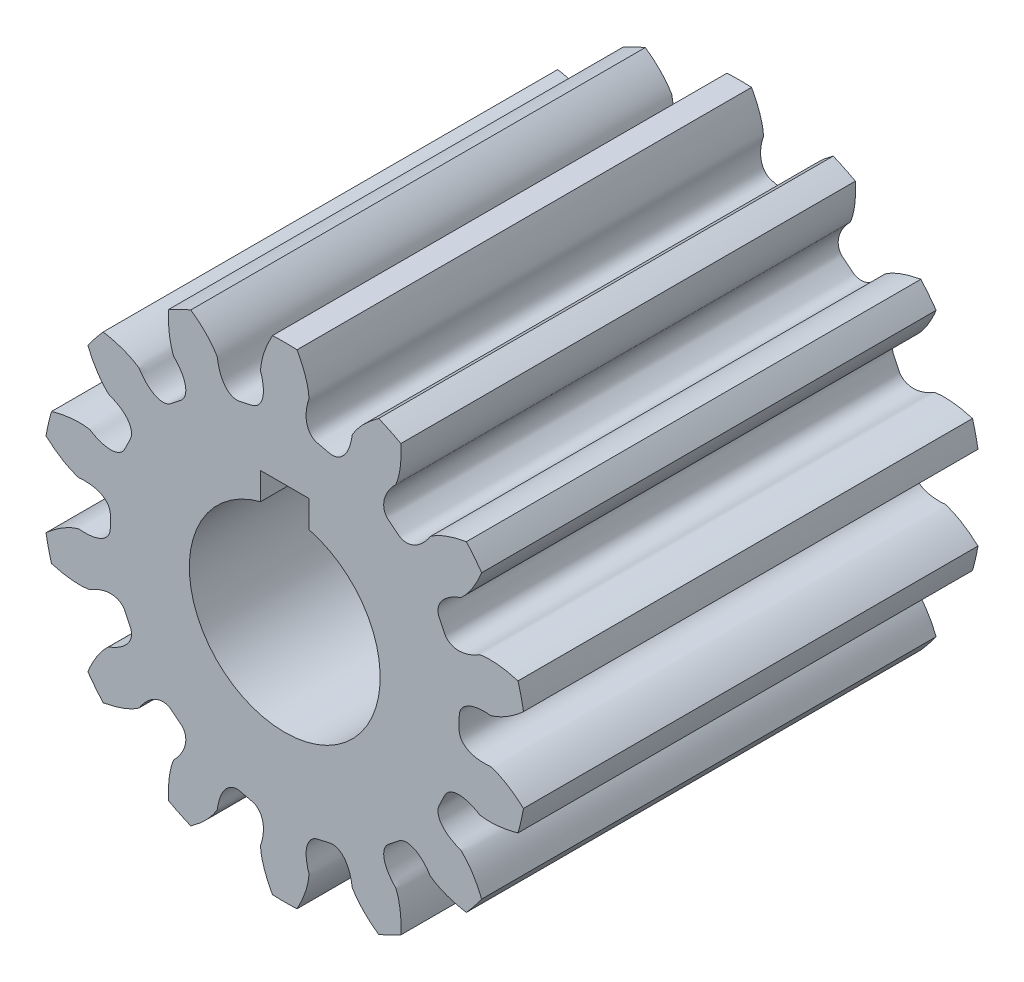
SolidWorks part; units mm, degrees
ref_plane "Front Plane" through (0, 0, 0) normal (0, 0, 1) x (1, 0, 0)
ref_plane "Top Plane" through (0, 0, 0) normal (0, 1, 0) x (1, 0, 0)
ref_plane "Right Plane" through (0, 0, 0) normal (1, 0, 0) x (0, 0, -1)
ref_plane "Plane1" through (0, 0, 9.525) normal (0, 0, 1) x (1, 0, 0)
sketch "Sketch1" plane through (0, 0, 9.525) normal (0, 0, 1) x (1, 0, 0)
  line L0 (1.01, 5) -> (1.01, 3.8704)
  line L1 (-1.01, 3.8704) -> (-1.01, 5)
  line L2 (-1.01, 5) -> (1.01, 5)
  arc A0 (1.01, 3.8704) -> (-1.01, 3.8704) centre (0, 0) cw
  arc A1 (8.2542, 5.9239) -> (7.6122, 6.7291) centre (0, 0) ccw
  arc A2 (4.8665, 8.9187) -> (3.9387, 9.3655) centre (0, 0) ccw
  arc A3 (0.5149, 10.1469) -> (-0.5149, 10.1469) centre (0, 0) ccw
  arc A4 (-3.9387, 9.3655) -> (-4.8665, 8.9187) centre (0, 0) ccw
  arc A5 (-7.6122, 6.7291) -> (-8.2542, 5.9239) centre (0, 0) ccw
  arc A6 (-9.778, 2.7599) -> (-10.0071, 1.7559) centre (0, 0) ccw
  arc A7 (-10.0071, -1.7559) -> (-9.778, -2.7599) centre (0, 0) ccw
  arc A8 (-8.2542, -5.9239) -> (-7.6122, -6.7291) centre (0, 0) ccw
  arc A9 (-4.8665, -8.9187) -> (-3.9387, -9.3655) centre (0, 0) ccw
  arc A10 (-0.5149, -10.1469) -> (0.5149, -10.1469) centre (0, 0) ccw
  arc A11 (3.9387, -9.3655) -> (4.8665, -8.9187) centre (0, 0) ccw
  arc A12 (7.6122, -6.7291) -> (8.2542, -5.9239) centre (0, 0) ccw
  arc A13 (9.778, -2.7599) -> (10.0071, -1.7559) centre (0, 0) ccw
  arc A14 (10.0071, 1.7559) -> (9.778, 2.7599) centre (0, 0) ccw
  spline S0 degree 3 poles (8.2542, 5.9239) (8.2213, 5.8435) (8.1658, 5.7165) (8.0838, 5.5483) (8.0156, 5.4193) (7.9477, 5.3002) (7.8807, 5.1908) (7.8151, 5.0911) (7.7514, 5.0008) (7.6901, 4.9196) (7.6319, 4.8472) (7.5771, 4.7835) (7.5263, 4.7282) (7.4801, 4.6804) (7.4277, 4.6319) (7.3617, 4.5626) (7.2605, 4.5412) (7.1763, 4.501) (7.1095, 4.4698) (7.046, 4.4368) (6.9852, 4.4028) (6.9274, 4.3677) (6.8725, 4.3315) (6.8204, 4.2943) (6.7711, 4.2559) (6.7247, 4.2165) (6.681, 4.1758) (6.64, 4.1337) (6.6019, 4.0902) (6.5666, 4.045) (6.5342, 3.9978) (6.5048, 3.9483) (6.4789, 3.8961) (6.4567, 3.8408) (6.4391, 3.782) (6.4268, 3.7194) (6.4213, 3.6531) (6.4238, 3.5836) (6.4357, 3.5122) (6.4562, 3.4476) (6.5069, 3.3338) (6.5953, 3.1761) (6.6635, 3.0087) (6.7208, 2.8982) (6.7585, 2.8418) (6.807, 2.788) (6.8597, 2.7427) (6.915, 2.7057) (6.9716, 2.6762) (7.0286, 2.6533) (7.0856, 2.6362) (7.1426, 2.6239) (7.1996, 2.616) (7.2567, 2.6119) (7.3141, 2.6114) (7.3719, 2.6141) (7.4303, 2.6199) (7.4893, 2.6286) (7.5492, 2.6404) (7.6099, 2.655) (7.6715, 2.6725) (7.734, 2.6929) (7.7975, 2.7162) (7.8619, 2.7424) (7.9273, 2.7715) (7.9934, 2.8043) (8.0773, 2.8451) (8.1571, 2.9109) (8.2524, 2.9193) (8.3231, 2.93) (8.3892, 2.9363) (8.4642, 2.9416) (8.5481, 2.9446) (8.641, 2.9451) (8.7427, 2.9423) (8.853, 2.9358) (8.9719, 2.9249) (9.0992, 2.9092) (9.2346, 2.888) (9.378, 2.8608) (9.5607, 2.8201) (9.6945, 2.7844) (9.778, 2.7599) knots 0.010403 0.010403 0.010403 0.010403 0.046486 0.067894 0.088079 0.107041 0.124779 0.141294 0.156585 0.170653 0.183498 0.19512 0.205518 0.214693 0.222644 0.235305 0.253444 0.263936 0.274129 0.28403 0.293651 0.303001 0.312093 0.320945 0.329573 0.337998 0.346246 0.354347 0.362336 0.370253 0.378149 0.386081 0.394114 0.402321 0.410779 0.419564 0.428738 0.438336 0.448346 0.458697 0.466397 0.5 0.533603 0.541303 0.551654 0.561664 0.571262 0.580436 0.589221 0.597679 0.605886 0.613919 0.621851 0.629747 0.637664 0.645653 0.653754 0.662002 0.670427 0.679055 0.687907 0.696999 0.706349 0.71597 0.725871 0.736064 0.746556 0.764695 0.777356 0.785307 0.794482 0.80488 0.816502 0.829347 0.843415 0.858706 0.875221 0.892959 0.911921 0.932106 0.953514 0.989597 0.989597 0.989597 0.989597
  spline S1 degree 3 poles (4.8665, 8.9187) (4.8718, 8.8319) (4.8769, 8.6934) (4.8759, 8.5062) (4.8705, 8.3604) (4.861, 8.2237) (4.848, 8.0961) (4.8322, 7.9778) (4.814, 7.8687) (4.7941, 7.769) (4.773, 7.6786) (4.7513, 7.5974) (4.7295, 7.5255) (4.7086, 7.4624) (4.6824, 7.3959) (4.653, 7.3049) (4.5711, 7.2417) (4.5127, 7.169) (4.466, 7.1119) (4.4231, 7.0545) (4.3832, 6.9976) (4.3463, 6.9409) (4.3125, 6.8844) (4.2818, 6.8283) (4.254, 6.7724) (4.2293, 6.7166) (4.2076, 6.661) (4.1889, 6.6054) (4.1734, 6.5496) (4.1612, 6.4936) (4.1525, 6.437) (4.1475, 6.3797) (4.1468, 6.3214) (4.1508, 6.2619) (4.1604, 6.2013) (4.1766, 6.1396) (4.2003, 6.0774) (4.2327, 6.0159) (4.2744, 5.9567) (4.321, 5.9074) (4.416, 5.8269) (4.5641, 5.7232) (4.6981, 5.6019) (4.7978, 5.5272) (4.8562, 5.4928) (4.9232, 5.4653) (4.9904, 5.4474) (5.0563, 5.4381) (5.12, 5.436) (5.1813, 5.4402) (5.2401, 5.4494) (5.2968, 5.4631) (5.3516, 5.4807) (5.4048, 5.5018) (5.4567, 5.5262) (5.5076, 5.5537) (5.5577, 5.5843) (5.6071, 5.6178) (5.656, 5.6543) (5.7043, 5.6938) (5.7522, 5.7363) (5.7997, 5.7818) (5.8468, 5.8304) (5.8934, 5.882) (5.9398, 5.9366) (5.985, 5.9948) (6.043, 6.0679) (6.0863, 6.1618) (6.1686, 6.2108) (6.2276, 6.2511) (6.2844, 6.2855) (6.3496, 6.3227) (6.424, 6.3619) (6.5074, 6.4026) (6.6002, 6.4442) (6.7025, 6.4862) (6.8143, 6.528) (6.9358, 6.5691) (7.067, 6.6087) (7.208, 6.6465) (7.3902, 6.6891) (7.5264, 6.7149) (7.6122, 6.7291) knots 0.010403 0.010403 0.010403 0.010403 0.046486 0.067894 0.088079 0.107041 0.124779 0.141294 0.156585 0.170653 0.183498 0.19512 0.205518 0.214693 0.222644 0.235305 0.253444 0.263936 0.274129 0.28403 0.293651 0.303001 0.312093 0.320945 0.329573 0.337998 0.346246 0.354347 0.362336 0.370253 0.378149 0.386081 0.394114 0.402321 0.410779 0.419564 0.428738 0.438336 0.448346 0.458697 0.466397 0.5 0.533603 0.541303 0.551654 0.561664 0.571262 0.580436 0.589221 0.597679 0.605886 0.613919 0.621851 0.629747 0.637664 0.645653 0.653754 0.662002 0.670427 0.679055 0.687907 0.696999 0.706349 0.71597 0.725871 0.736064 0.746556 0.764695 0.777356 0.785307 0.794482 0.80488 0.816502 0.829347 0.843415 0.858706 0.875221 0.892959 0.911921 0.932106 0.953514 0.989597 0.989597 0.989597 0.989597
  spline S2 degree 3 poles (0.5149, 10.1469) (0.5573, 10.071) (0.622, 9.9485) (0.7023, 9.7794) (0.7607, 9.6457) (0.8115, 9.5184) (0.8552, 9.3978) (0.8922, 9.2843) (0.9231, 9.1782) (0.9485, 9.0797) (0.9687, 8.9891) (0.9844, 8.9065) (0.9959, 8.8323) (1.0044, 8.7664) (1.0098, 8.6951) (1.0228, 8.6003) (0.9764, 8.5079) (0.9553, 8.417) (0.938, 8.3453) (0.9243, 8.275) (0.913, 8.2064) (0.9044, 8.1393) (0.8984, 8.0738) (0.8951, 8.0099) (0.8943, 7.9474) (0.8962, 7.8865) (0.9008, 7.8269) (0.9081, 7.7687) (0.9183, 7.7118) (0.9317, 7.656) (0.9483, 7.6012) (0.9688, 7.5474) (0.9934, 7.4946) (1.0228, 7.4428) (1.0578, 7.3923) (1.0991, 7.3437) (1.1475, 7.298) (1.2034, 7.2567) (1.2666, 7.2215) (1.33, 7.1972) (1.4505, 7.1659) (1.6289, 7.1367) (1.8023, 7.0856) (1.9245, 7.0615) (1.9921, 7.0559) (2.0644, 7.0602) (2.1327, 7.0732) (2.1961, 7.0934) (2.2544, 7.1192) (2.3078, 7.1495) (2.3568, 7.1834) (2.4019, 7.2203) (2.4436, 7.2599) (2.4824, 7.302) (2.5186, 7.3465) (2.5526, 7.3934) (2.5844, 7.4427) (2.6144, 7.4943) (2.6425, 7.5484) (2.6689, 7.605) (2.6937, 7.6641) (2.7167, 7.7257) (2.7381, 7.7898) (2.7577, 7.8566) (2.7758, 7.9259) (2.7913, 7.998) (2.8117, 8.089) (2.8101, 8.1924) (2.8629, 8.2722) (2.8986, 8.3341) (2.9349, 8.3897) (2.9775, 8.4516) (3.0275, 8.5192) (3.085, 8.592) (3.1505, 8.6698) (3.2245, 8.752) (3.3071, 8.8382) (3.3987, 8.9279) (3.4997, 9.0205) (3.6104, 9.1157) (3.7561, 9.2331) (3.8675, 9.3155) (3.9387, 9.3655) knots 0.010403 0.010403 0.010403 0.010403 0.046486 0.067894 0.088079 0.107041 0.124779 0.141294 0.156585 0.170653 0.183498 0.19512 0.205518 0.214693 0.222644 0.235305 0.253444 0.263936 0.274129 0.28403 0.293651 0.303001 0.312093 0.320945 0.329573 0.337998 0.346246 0.354347 0.362336 0.370253 0.378149 0.386081 0.394114 0.402321 0.410779 0.419564 0.428738 0.438336 0.448346 0.458697 0.466397 0.5 0.533603 0.541303 0.551654 0.561664 0.571262 0.580436 0.589221 0.597679 0.605886 0.613919 0.621851 0.629747 0.637664 0.645653 0.653754 0.662002 0.670427 0.679055 0.687907 0.696999 0.706349 0.71597 0.725871 0.736064 0.746556 0.764695 0.777356 0.785307 0.794482 0.80488 0.816502 0.829347 0.843415 0.858706 0.875221 0.892959 0.911921 0.932106 0.953514 0.989597 0.989597 0.989597 0.989597
  spline S3 degree 3 poles (-3.9387, 9.3655) (-3.8675, 9.3155) (-3.7561, 9.2331) (-3.6104, 9.1157) (-3.4997, 9.0205) (-3.3987, 8.9279) (-3.3071, 8.8382) (-3.2245, 8.752) (-3.1505, 8.6698) (-3.085, 8.592) (-3.0275, 8.5192) (-2.9775, 8.4516) (-2.9349, 8.3897) (-2.8986, 8.3341) (-2.8629, 8.2722) (-2.8101, 8.1924) (-2.8117, 8.089) (-2.7913, 7.998) (-2.7758, 7.9259) (-2.7577, 7.8566) (-2.7381, 7.7898) (-2.7167, 7.7257) (-2.6937, 7.6641) (-2.6689, 7.605) (-2.6425, 7.5484) (-2.6144, 7.4943) (-2.5844, 7.4427) (-2.5526, 7.3934) (-2.5186, 7.3465) (-2.4824, 7.302) (-2.4436, 7.2599) (-2.4019, 7.2203) (-2.3568, 7.1834) (-2.3078, 7.1495) (-2.2544, 7.1192) (-2.1961, 7.0934) (-2.1327, 7.0732) (-2.0644, 7.0602) (-1.9921, 7.0559) (-1.9245, 7.0615) (-1.8023, 7.0856) (-1.6289, 7.1367) (-1.4505, 7.1659) (-1.33, 7.1972) (-1.2666, 7.2215) (-1.2034, 7.2567) (-1.1475, 7.298) (-1.0991, 7.3437) (-1.0578, 7.3923) (-1.0228, 7.4428) (-0.9934, 7.4946) (-0.9688, 7.5474) (-0.9483, 7.6012) (-0.9317, 7.656) (-0.9183, 7.7118) (-0.9081, 7.7687) (-0.9008, 7.8269) (-0.8962, 7.8865) (-0.8943, 7.9474) (-0.8951, 8.0099) (-0.8984, 8.0738) (-0.9044, 8.1393) (-0.913, 8.2064) (-0.9243, 8.275) (-0.938, 8.3453) (-0.9553, 8.417) (-0.9764, 8.5079) (-1.0228, 8.6003) (-1.0098, 8.6951) (-1.0044, 8.7664) (-0.9959, 8.8323) (-0.9844, 8.9065) (-0.9687, 8.9891) (-0.9485, 9.0797) (-0.9231, 9.1782) (-0.8922, 9.2843) (-0.8552, 9.3978) (-0.8115, 9.5184) (-0.7607, 9.6457) (-0.7023, 9.7794) (-0.622, 9.9485) (-0.5573, 10.071) (-0.5149, 10.1469) knots 0.010403 0.010403 0.010403 0.010403 0.046486 0.067894 0.088079 0.107041 0.124779 0.141294 0.156585 0.170653 0.183498 0.19512 0.205518 0.214693 0.222644 0.235305 0.253444 0.263936 0.274129 0.28403 0.293651 0.303001 0.312093 0.320945 0.329573 0.337998 0.346246 0.354347 0.362336 0.370253 0.378149 0.386081 0.394114 0.402321 0.410779 0.419564 0.428738 0.438336 0.448346 0.458697 0.466397 0.5 0.533603 0.541303 0.551654 0.561664 0.571262 0.580436 0.589221 0.597679 0.605886 0.613919 0.621851 0.629747 0.637664 0.645653 0.653754 0.662002 0.670427 0.679055 0.687907 0.696999 0.706349 0.71597 0.725871 0.736064 0.746556 0.764695 0.777356 0.785307 0.794482 0.80488 0.816502 0.829347 0.843415 0.858706 0.875221 0.892959 0.911921 0.932106 0.953514 0.989597 0.989597 0.989597 0.989597
  spline S4 degree 3 poles (-7.6122, 6.7291) (-7.5264, 6.7149) (-7.3902, 6.6891) (-7.208, 6.6465) (-7.067, 6.6087) (-6.9358, 6.5691) (-6.8143, 6.528) (-6.7025, 6.4862) (-6.6002, 6.4442) (-6.5074, 6.4026) (-6.424, 6.3619) (-6.3496, 6.3227) (-6.2844, 6.2855) (-6.2276, 6.2511) (-6.1686, 6.2108) (-6.0863, 6.1618) (-6.043, 6.0679) (-5.985, 5.9948) (-5.9398, 5.9366) (-5.8934, 5.882) (-5.8468, 5.8304) (-5.7997, 5.7818) (-5.7522, 5.7363) (-5.7043, 5.6938) (-5.656, 5.6543) (-5.6071, 5.6178) (-5.5577, 5.5843) (-5.5076, 5.5537) (-5.4567, 5.5262) (-5.4048, 5.5018) (-5.3516, 5.4807) (-5.2968, 5.4631) (-5.2401, 5.4494) (-5.1813, 5.4402) (-5.12, 5.436) (-5.0563, 5.4381) (-4.9904, 5.4474) (-4.9232, 5.4653) (-4.8562, 5.4928) (-4.7978, 5.5272) (-4.6981, 5.6019) (-4.5641, 5.7232) (-4.416, 5.8269) (-4.321, 5.9074) (-4.2744, 5.9567) (-4.2327, 6.0159) (-4.2003, 6.0774) (-4.1766, 6.1396) (-4.1604, 6.2013) (-4.1508, 6.2619) (-4.1468, 6.3214) (-4.1475, 6.3797) (-4.1525, 6.437) (-4.1612, 6.4936) (-4.1734, 6.5496) (-4.1889, 6.6054) (-4.2076, 6.661) (-4.2293, 6.7166) (-4.254, 6.7724) (-4.2818, 6.8283) (-4.3125, 6.8844) (-4.3463, 6.9409) (-4.3832, 6.9976) (-4.4231, 7.0545) (-4.466, 7.1119) (-4.5127, 7.169) (-4.5711, 7.2417) (-4.653, 7.3049) (-4.6824, 7.3959) (-4.7086, 7.4624) (-4.7295, 7.5255) (-4.7513, 7.5974) (-4.773, 7.6786) (-4.7941, 7.769) (-4.814, 7.8687) (-4.8322, 7.9778) (-4.848, 8.0961) (-4.861, 8.2237) (-4.8705, 8.3604) (-4.8759, 8.5062) (-4.8769, 8.6934) (-4.8718, 8.8319) (-4.8665, 8.9187) knots 0.010403 0.010403 0.010403 0.010403 0.046486 0.067894 0.088079 0.107041 0.124779 0.141294 0.156585 0.170653 0.183498 0.19512 0.205518 0.214693 0.222644 0.235305 0.253444 0.263936 0.274129 0.28403 0.293651 0.303001 0.312093 0.320945 0.329573 0.337998 0.346246 0.354347 0.362336 0.370253 0.378149 0.386081 0.394114 0.402321 0.410779 0.419564 0.428738 0.438336 0.448346 0.458697 0.466397 0.5 0.533603 0.541303 0.551654 0.561664 0.571262 0.580436 0.589221 0.597679 0.605886 0.613919 0.621851 0.629747 0.637664 0.645653 0.653754 0.662002 0.670427 0.679055 0.687907 0.696999 0.706349 0.71597 0.725871 0.736064 0.746556 0.764695 0.777356 0.785307 0.794482 0.80488 0.816502 0.829347 0.843415 0.858706 0.875221 0.892959 0.911921 0.932106 0.953514 0.989597 0.989597 0.989597 0.989597
  spline S5 degree 3 poles (-9.778, 2.7599) (-9.6945, 2.7844) (-9.5607, 2.8201) (-9.378, 2.8608) (-9.2346, 2.888) (-9.0992, 2.9092) (-8.9719, 2.9249) (-8.853, 2.9358) (-8.7427, 2.9423) (-8.641, 2.9451) (-8.5481, 2.9446) (-8.4642, 2.9416) (-8.3892, 2.9363) (-8.3231, 2.93) (-8.2524, 2.9193) (-8.1571, 2.9109) (-8.0773, 2.8451) (-7.9934, 2.8043) (-7.9273, 2.7715) (-7.8619, 2.7424) (-7.7975, 2.7162) (-7.734, 2.6929) (-7.6715, 2.6725) (-7.6099, 2.655) (-7.5492, 2.6404) (-7.4893, 2.6286) (-7.4303, 2.6199) (-7.3719, 2.6141) (-7.3141, 2.6114) (-7.2567, 2.6119) (-7.1996, 2.616) (-7.1426, 2.6239) (-7.0856, 2.6362) (-7.0286, 2.6533) (-6.9716, 2.6762) (-6.915, 2.7057) (-6.8597, 2.7427) (-6.807, 2.788) (-6.7585, 2.8418) (-6.7208, 2.8982) (-6.6635, 3.0087) (-6.5953, 3.1761) (-6.5069, 3.3338) (-6.4562, 3.4476) (-6.4357, 3.5122) (-6.4238, 3.5836) (-6.4213, 3.6531) (-6.4268, 3.7194) (-6.4391, 3.782) (-6.4567, 3.8408) (-6.4789, 3.8961) (-6.5048, 3.9483) (-6.5342, 3.9978) (-6.5666, 4.045) (-6.6019, 4.0902) (-6.64, 4.1337) (-6.681, 4.1758) (-6.7247, 4.2165) (-6.7711, 4.2559) (-6.8204, 4.2943) (-6.8725, 4.3315) (-6.9274, 4.3677) (-6.9852, 4.4028) (-7.046, 4.4368) (-7.1095, 4.4698) (-7.1763, 4.501) (-7.2605, 4.5412) (-7.3617, 4.5626) (-7.4277, 4.6319) (-7.4801, 4.6804) (-7.5263, 4.7282) (-7.5771, 4.7835) (-7.6319, 4.8472) (-7.6901, 4.9196) (-7.7514, 5.0008) (-7.8151, 5.0911) (-7.8807, 5.1908) (-7.9477, 5.3002) (-8.0156, 5.4193) (-8.0838, 5.5483) (-8.1658, 5.7165) (-8.2213, 5.8435) (-8.2542, 5.9239) knots 0.010403 0.010403 0.010403 0.010403 0.046486 0.067894 0.088079 0.107041 0.124779 0.141294 0.156585 0.170653 0.183498 0.19512 0.205518 0.214693 0.222644 0.235305 0.253444 0.263936 0.274129 0.28403 0.293651 0.303001 0.312093 0.320945 0.329573 0.337998 0.346246 0.354347 0.362336 0.370253 0.378149 0.386081 0.394114 0.402321 0.410779 0.419564 0.428738 0.438336 0.448346 0.458697 0.466397 0.5 0.533603 0.541303 0.551654 0.561664 0.571262 0.580436 0.589221 0.597679 0.605886 0.613919 0.621851 0.629747 0.637664 0.645653 0.653754 0.662002 0.670427 0.679055 0.687907 0.696999 0.706349 0.71597 0.725871 0.736064 0.746556 0.764695 0.777356 0.785307 0.794482 0.80488 0.816502 0.829347 0.843415 0.858706 0.875221 0.892959 0.911921 0.932106 0.953514 0.989597 0.989597 0.989597 0.989597
  spline S6 degree 3 poles (-10.0071, -1.7559) (-9.9426, -1.6977) (-9.8375, -1.6074) (-9.6905, -1.4914) (-9.5731, -1.4047) (-9.4603, -1.3269) (-9.3525, -1.2575) (-9.2501, -1.1961) (-9.1535, -1.1423) (-9.0631, -1.0957) (-8.9792, -1.0559) (-8.9023, -1.0222) (-8.8324, -0.9944) (-8.7701, -0.9714) (-8.7018, -0.9504) (-8.6123, -0.9166) (-8.5118, -0.9413) (-8.4186, -0.9416) (-8.3448, -0.9425) (-8.2732, -0.9403) (-8.2038, -0.936) (-8.1365, -0.9295) (-8.0713, -0.9207) (-8.0082, -0.9097) (-7.9472, -0.8966) (-7.8882, -0.8812) (-7.8311, -0.8635) (-7.776, -0.8434) (-7.7228, -0.8207) (-7.6713, -0.7953) (-7.6217, -0.7669) (-7.5738, -0.735) (-7.5277, -0.6992) (-7.4838, -0.659) (-7.4423, -0.6137) (-7.4042, -0.5626) (-7.3704, -0.5053) (-7.3425, -0.4416) (-7.3222, -0.3721) (-7.3127, -0.3049) (-7.309, -0.1804) (-7.3203, 0) (-7.309, 0.1804) (-7.3127, 0.3049) (-7.3222, 0.3721) (-7.3425, 0.4416) (-7.3704, 0.5053) (-7.4042, 0.5626) (-7.4423, 0.6137) (-7.4838, 0.659) (-7.5277, 0.6992) (-7.5738, 0.735) (-7.6217, 0.7669) (-7.6713, 0.7953) (-7.7228, 0.8207) (-7.776, 0.8434) (-7.8311, 0.8635) (-7.8882, 0.8812) (-7.9472, 0.8966) (-8.0082, 0.9097) (-8.0713, 0.9207) (-8.1365, 0.9295) (-8.2038, 0.936) (-8.2732, 0.9403) (-8.3448, 0.9425) (-8.4186, 0.9416) (-8.5118, 0.9413) (-8.6123, 0.9166) (-8.7018, 0.9504) (-8.7701, 0.9714) (-8.8324, 0.9944) (-8.9023, 1.0222) (-8.9792, 1.0559) (-9.0631, 1.0957) (-9.1535, 1.1423) (-9.2501, 1.1961) (-9.3525, 1.2575) (-9.4603, 1.3269) (-9.5731, 1.4047) (-9.6905, 1.4914) (-9.8375, 1.6074) (-9.9426, 1.6977) (-10.0071, 1.7559) knots 0.010403 0.010403 0.010403 0.010403 0.046486 0.067894 0.088079 0.107041 0.124779 0.141294 0.156585 0.170653 0.183498 0.19512 0.205518 0.214693 0.222644 0.235305 0.253444 0.263936 0.274129 0.28403 0.293651 0.303001 0.312093 0.320945 0.329573 0.337998 0.346246 0.354347 0.362336 0.370253 0.378149 0.386081 0.394114 0.402321 0.410779 0.419564 0.428738 0.438336 0.448346 0.458697 0.466397 0.5 0.533603 0.541303 0.551654 0.561664 0.571262 0.580436 0.589221 0.597679 0.605886 0.613919 0.621851 0.629747 0.637664 0.645653 0.653754 0.662002 0.670427 0.679055 0.687907 0.696999 0.706349 0.71597 0.725871 0.736064 0.746556 0.764695 0.777356 0.785307 0.794482 0.80488 0.816502 0.829347 0.843415 0.858706 0.875221 0.892959 0.911921 0.932106 0.953514 0.989597 0.989597 0.989597 0.989597
  spline S7 degree 3 poles (-8.2542, -5.9239) (-8.2213, -5.8435) (-8.1658, -5.7165) (-8.0838, -5.5483) (-8.0156, -5.4193) (-7.9477, -5.3002) (-7.8807, -5.1908) (-7.8151, -5.0911) (-7.7514, -5.0008) (-7.6901, -4.9196) (-7.6319, -4.8472) (-7.5771, -4.7835) (-7.5263, -4.7282) (-7.4801, -4.6804) (-7.4277, -4.6319) (-7.3617, -4.5626) (-7.2605, -4.5412) (-7.1763, -4.501) (-7.1095, -4.4698) (-7.046, -4.4368) (-6.9852, -4.4028) (-6.9274, -4.3677) (-6.8725, -4.3315) (-6.8204, -4.2943) (-6.7711, -4.2559) (-6.7247, -4.2165) (-6.681, -4.1758) (-6.64, -4.1337) (-6.6019, -4.0902) (-6.5666, -4.045) (-6.5342, -3.9978) (-6.5048, -3.9483) (-6.4789, -3.8961) (-6.4567, -3.8408) (-6.4391, -3.782) (-6.4268, -3.7194) (-6.4213, -3.6531) (-6.4238, -3.5836) (-6.4357, -3.5122) (-6.4562, -3.4476) (-6.5069, -3.3338) (-6.5953, -3.1761) (-6.6635, -3.0087) (-6.7208, -2.8982) (-6.7585, -2.8418) (-6.807, -2.788) (-6.8597, -2.7427) (-6.915, -2.7057) (-6.9716, -2.6762) (-7.0286, -2.6533) (-7.0856, -2.6362) (-7.1426, -2.6239) (-7.1996, -2.616) (-7.2567, -2.6119) (-7.3141, -2.6114) (-7.3719, -2.6141) (-7.4303, -2.6199) (-7.4893, -2.6286) (-7.5492, -2.6404) (-7.6099, -2.655) (-7.6715, -2.6725) (-7.734, -2.6929) (-7.7975, -2.7162) (-7.8619, -2.7424) (-7.9273, -2.7715) (-7.9934, -2.8043) (-8.0773, -2.8451) (-8.1571, -2.9109) (-8.2524, -2.9193) (-8.3231, -2.93) (-8.3892, -2.9363) (-8.4642, -2.9416) (-8.5481, -2.9446) (-8.641, -2.9451) (-8.7427, -2.9423) (-8.853, -2.9358) (-8.9719, -2.9249) (-9.0992, -2.9092) (-9.2346, -2.888) (-9.378, -2.8608) (-9.5607, -2.8201) (-9.6945, -2.7844) (-9.778, -2.7599) knots 0.010403 0.010403 0.010403 0.010403 0.046486 0.067894 0.088079 0.107041 0.124779 0.141294 0.156585 0.170653 0.183498 0.19512 0.205518 0.214693 0.222644 0.235305 0.253444 0.263936 0.274129 0.28403 0.293651 0.303001 0.312093 0.320945 0.329573 0.337998 0.346246 0.354347 0.362336 0.370253 0.378149 0.386081 0.394114 0.402321 0.410779 0.419564 0.428738 0.438336 0.448346 0.458697 0.466397 0.5 0.533603 0.541303 0.551654 0.561664 0.571262 0.580436 0.589221 0.597679 0.605886 0.613919 0.621851 0.629747 0.637664 0.645653 0.653754 0.662002 0.670427 0.679055 0.687907 0.696999 0.706349 0.71597 0.725871 0.736064 0.746556 0.764695 0.777356 0.785307 0.794482 0.80488 0.816502 0.829347 0.843415 0.858706 0.875221 0.892959 0.911921 0.932106 0.953514 0.989597 0.989597 0.989597 0.989597
  spline S8 degree 3 poles (-4.8665, -8.9187) (-4.8718, -8.8319) (-4.8769, -8.6934) (-4.8759, -8.5062) (-4.8705, -8.3604) (-4.861, -8.2237) (-4.848, -8.0961) (-4.8322, -7.9778) (-4.814, -7.8687) (-4.7941, -7.769) (-4.773, -7.6786) (-4.7513, -7.5974) (-4.7295, -7.5255) (-4.7086, -7.4624) (-4.6824, -7.3959) (-4.653, -7.3049) (-4.5711, -7.2417) (-4.5127, -7.169) (-4.466, -7.1119) (-4.4231, -7.0545) (-4.3832, -6.9976) (-4.3463, -6.9409) (-4.3125, -6.8844) (-4.2818, -6.8283) (-4.254, -6.7724) (-4.2293, -6.7166) (-4.2076, -6.661) (-4.1889, -6.6054) (-4.1734, -6.5496) (-4.1612, -6.4936) (-4.1525, -6.437) (-4.1475, -6.3797) (-4.1468, -6.3214) (-4.1508, -6.2619) (-4.1604, -6.2013) (-4.1766, -6.1396) (-4.2003, -6.0774) (-4.2327, -6.0159) (-4.2744, -5.9567) (-4.321, -5.9074) (-4.416, -5.8269) (-4.5641, -5.7232) (-4.6981, -5.6019) (-4.7978, -5.5272) (-4.8562, -5.4928) (-4.9232, -5.4653) (-4.9904, -5.4474) (-5.0563, -5.4381) (-5.12, -5.436) (-5.1813, -5.4402) (-5.2401, -5.4494) (-5.2968, -5.4631) (-5.3516, -5.4807) (-5.4048, -5.5018) (-5.4567, -5.5262) (-5.5076, -5.5537) (-5.5577, -5.5843) (-5.6071, -5.6178) (-5.656, -5.6543) (-5.7043, -5.6938) (-5.7522, -5.7363) (-5.7997, -5.7818) (-5.8468, -5.8304) (-5.8934, -5.882) (-5.9398, -5.9366) (-5.985, -5.9948) (-6.043, -6.0679) (-6.0863, -6.1618) (-6.1686, -6.2108) (-6.2276, -6.2511) (-6.2844, -6.2855) (-6.3496, -6.3227) (-6.424, -6.3619) (-6.5074, -6.4026) (-6.6002, -6.4442) (-6.7025, -6.4862) (-6.8143, -6.528) (-6.9358, -6.5691) (-7.067, -6.6087) (-7.208, -6.6465) (-7.3902, -6.6891) (-7.5264, -6.7149) (-7.6122, -6.7291) knots 0.010403 0.010403 0.010403 0.010403 0.046486 0.067894 0.088079 0.107041 0.124779 0.141294 0.156585 0.170653 0.183498 0.19512 0.205518 0.214693 0.222644 0.235305 0.253444 0.263936 0.274129 0.28403 0.293651 0.303001 0.312093 0.320945 0.329573 0.337998 0.346246 0.354347 0.362336 0.370253 0.378149 0.386081 0.394114 0.402321 0.410779 0.419564 0.428738 0.438336 0.448346 0.458697 0.466397 0.5 0.533603 0.541303 0.551654 0.561664 0.571262 0.580436 0.589221 0.597679 0.605886 0.613919 0.621851 0.629747 0.637664 0.645653 0.653754 0.662002 0.670427 0.679055 0.687907 0.696999 0.706349 0.71597 0.725871 0.736064 0.746556 0.764695 0.777356 0.785307 0.794482 0.80488 0.816502 0.829347 0.843415 0.858706 0.875221 0.892959 0.911921 0.932106 0.953514 0.989597 0.989597 0.989597 0.989597
  spline S9 degree 3 poles (-0.5149, -10.1469) (-0.5573, -10.071) (-0.622, -9.9485) (-0.7023, -9.7794) (-0.7607, -9.6457) (-0.8115, -9.5184) (-0.8552, -9.3978) (-0.8922, -9.2843) (-0.9231, -9.1782) (-0.9485, -9.0797) (-0.9687, -8.9891) (-0.9844, -8.9065) (-0.9959, -8.8323) (-1.0044, -8.7664) (-1.0098, -8.6951) (-1.0228, -8.6003) (-0.9764, -8.5079) (-0.9553, -8.417) (-0.938, -8.3453) (-0.9243, -8.275) (-0.913, -8.2064) (-0.9044, -8.1393) (-0.8984, -8.0738) (-0.8951, -8.0099) (-0.8943, -7.9474) (-0.8962, -7.8865) (-0.9008, -7.8269) (-0.9081, -7.7687) (-0.9183, -7.7118) (-0.9317, -7.656) (-0.9483, -7.6012) (-0.9688, -7.5474) (-0.9934, -7.4946) (-1.0228, -7.4428) (-1.0578, -7.3923) (-1.0991, -7.3437) (-1.1475, -7.298) (-1.2034, -7.2567) (-1.2666, -7.2215) (-1.33, -7.1972) (-1.4505, -7.1659) (-1.6289, -7.1367) (-1.8023, -7.0856) (-1.9245, -7.0615) (-1.9921, -7.0559) (-2.0644, -7.0602) (-2.1327, -7.0732) (-2.1961, -7.0934) (-2.2544, -7.1192) (-2.3078, -7.1495) (-2.3568, -7.1834) (-2.4019, -7.2203) (-2.4436, -7.2599) (-2.4824, -7.302) (-2.5186, -7.3465) (-2.5526, -7.3934) (-2.5844, -7.4427) (-2.6144, -7.4943) (-2.6425, -7.5484) (-2.6689, -7.605) (-2.6937, -7.6641) (-2.7167, -7.7257) (-2.7381, -7.7898) (-2.7577, -7.8566) (-2.7758, -7.9259) (-2.7913, -7.998) (-2.8117, -8.089) (-2.8101, -8.1924) (-2.8629, -8.2722) (-2.8986, -8.3341) (-2.9349, -8.3897) (-2.9775, -8.4516) (-3.0275, -8.5192) (-3.085, -8.592) (-3.1505, -8.6698) (-3.2245, -8.752) (-3.3071, -8.8382) (-3.3987, -8.9279) (-3.4997, -9.0205) (-3.6104, -9.1157) (-3.7561, -9.2331) (-3.8675, -9.3155) (-3.9387, -9.3655) knots 0.010403 0.010403 0.010403 0.010403 0.046486 0.067894 0.088079 0.107041 0.124779 0.141294 0.156585 0.170653 0.183498 0.19512 0.205518 0.214693 0.222644 0.235305 0.253444 0.263936 0.274129 0.28403 0.293651 0.303001 0.312093 0.320945 0.329573 0.337998 0.346246 0.354347 0.362336 0.370253 0.378149 0.386081 0.394114 0.402321 0.410779 0.419564 0.428738 0.438336 0.448346 0.458697 0.466397 0.5 0.533603 0.541303 0.551654 0.561664 0.571262 0.580436 0.589221 0.597679 0.605886 0.613919 0.621851 0.629747 0.637664 0.645653 0.653754 0.662002 0.670427 0.679055 0.687907 0.696999 0.706349 0.71597 0.725871 0.736064 0.746556 0.764695 0.777356 0.785307 0.794482 0.80488 0.816502 0.829347 0.843415 0.858706 0.875221 0.892959 0.911921 0.932106 0.953514 0.989597 0.989597 0.989597 0.989597
  spline S10 degree 3 poles (3.9387, -9.3655) (3.8675, -9.3155) (3.7561, -9.2331) (3.6104, -9.1157) (3.4997, -9.0205) (3.3987, -8.9279) (3.3071, -8.8382) (3.2245, -8.752) (3.1505, -8.6698) (3.085, -8.592) (3.0275, -8.5192) (2.9775, -8.4516) (2.9349, -8.3897) (2.8986, -8.3341) (2.8629, -8.2722) (2.8101, -8.1924) (2.8117, -8.089) (2.7913, -7.998) (2.7758, -7.9259) (2.7577, -7.8566) (2.7381, -7.7898) (2.7167, -7.7257) (2.6937, -7.6641) (2.6689, -7.605) (2.6425, -7.5484) (2.6144, -7.4943) (2.5844, -7.4427) (2.5526, -7.3934) (2.5186, -7.3465) (2.4824, -7.302) (2.4436, -7.2599) (2.4019, -7.2203) (2.3568, -7.1834) (2.3078, -7.1495) (2.2544, -7.1192) (2.1961, -7.0934) (2.1327, -7.0732) (2.0644, -7.0602) (1.9921, -7.0559) (1.9245, -7.0615) (1.8023, -7.0856) (1.6289, -7.1367) (1.4505, -7.1659) (1.33, -7.1972) (1.2666, -7.2215) (1.2034, -7.2567) (1.1475, -7.298) (1.0991, -7.3437) (1.0578, -7.3923) (1.0228, -7.4428) (0.9934, -7.4946) (0.9688, -7.5474) (0.9483, -7.6012) (0.9317, -7.656) (0.9183, -7.7118) (0.9081, -7.7687) (0.9008, -7.8269) (0.8962, -7.8865) (0.8943, -7.9474) (0.8951, -8.0099) (0.8984, -8.0738) (0.9044, -8.1393) (0.913, -8.2064) (0.9243, -8.275) (0.938, -8.3453) (0.9553, -8.417) (0.9764, -8.5079) (1.0228, -8.6003) (1.0098, -8.6951) (1.0044, -8.7664) (0.9959, -8.8323) (0.9844, -8.9065) (0.9687, -8.9891) (0.9485, -9.0797) (0.9231, -9.1782) (0.8922, -9.2843) (0.8552, -9.3978) (0.8115, -9.5184) (0.7607, -9.6457) (0.7023, -9.7794) (0.622, -9.9485) (0.5573, -10.071) (0.5149, -10.1469) knots 0.010403 0.010403 0.010403 0.010403 0.046486 0.067894 0.088079 0.107041 0.124779 0.141294 0.156585 0.170653 0.183498 0.19512 0.205518 0.214693 0.222644 0.235305 0.253444 0.263936 0.274129 0.28403 0.293651 0.303001 0.312093 0.320945 0.329573 0.337998 0.346246 0.354347 0.362336 0.370253 0.378149 0.386081 0.394114 0.402321 0.410779 0.419564 0.428738 0.438336 0.448346 0.458697 0.466397 0.5 0.533603 0.541303 0.551654 0.561664 0.571262 0.580436 0.589221 0.597679 0.605886 0.613919 0.621851 0.629747 0.637664 0.645653 0.653754 0.662002 0.670427 0.679055 0.687907 0.696999 0.706349 0.71597 0.725871 0.736064 0.746556 0.764695 0.777356 0.785307 0.794482 0.80488 0.816502 0.829347 0.843415 0.858706 0.875221 0.892959 0.911921 0.932106 0.953514 0.989597 0.989597 0.989597 0.989597
  spline S11 degree 3 poles (7.6122, -6.7291) (7.5264, -6.7149) (7.3902, -6.6891) (7.208, -6.6465) (7.067, -6.6087) (6.9358, -6.5691) (6.8143, -6.528) (6.7025, -6.4862) (6.6002, -6.4442) (6.5074, -6.4026) (6.424, -6.3619) (6.3496, -6.3227) (6.2844, -6.2855) (6.2276, -6.2511) (6.1686, -6.2108) (6.0863, -6.1618) (6.043, -6.0679) (5.985, -5.9948) (5.9398, -5.9366) (5.8934, -5.882) (5.8468, -5.8304) (5.7997, -5.7818) (5.7522, -5.7363) (5.7043, -5.6938) (5.656, -5.6543) (5.6071, -5.6178) (5.5577, -5.5843) (5.5076, -5.5537) (5.4567, -5.5262) (5.4048, -5.5018) (5.3516, -5.4807) (5.2968, -5.4631) (5.2401, -5.4494) (5.1813, -5.4402) (5.12, -5.436) (5.0563, -5.4381) (4.9904, -5.4474) (4.9232, -5.4653) (4.8562, -5.4928) (4.7978, -5.5272) (4.6981, -5.6019) (4.5641, -5.7232) (4.416, -5.8269) (4.321, -5.9074) (4.2744, -5.9567) (4.2327, -6.0159) (4.2003, -6.0774) (4.1766, -6.1396) (4.1604, -6.2013) (4.1508, -6.2619) (4.1468, -6.3214) (4.1475, -6.3797) (4.1525, -6.437) (4.1612, -6.4936) (4.1734, -6.5496) (4.1889, -6.6054) (4.2076, -6.661) (4.2293, -6.7166) (4.254, -6.7724) (4.2818, -6.8283) (4.3125, -6.8844) (4.3463, -6.9409) (4.3832, -6.9976) (4.4231, -7.0545) (4.466, -7.1119) (4.5127, -7.169) (4.5711, -7.2417) (4.653, -7.3049) (4.6824, -7.3959) (4.7086, -7.4624) (4.7295, -7.5255) (4.7513, -7.5974) (4.773, -7.6786) (4.7941, -7.769) (4.814, -7.8687) (4.8322, -7.9778) (4.848, -8.0961) (4.861, -8.2237) (4.8705, -8.3604) (4.8759, -8.5062) (4.8769, -8.6934) (4.8718, -8.8319) (4.8665, -8.9187) knots 0.010403 0.010403 0.010403 0.010403 0.046486 0.067894 0.088079 0.107041 0.124779 0.141294 0.156585 0.170653 0.183498 0.19512 0.205518 0.214693 0.222644 0.235305 0.253444 0.263936 0.274129 0.28403 0.293651 0.303001 0.312093 0.320945 0.329573 0.337998 0.346246 0.354347 0.362336 0.370253 0.378149 0.386081 0.394114 0.402321 0.410779 0.419564 0.428738 0.438336 0.448346 0.458697 0.466397 0.5 0.533603 0.541303 0.551654 0.561664 0.571262 0.580436 0.589221 0.597679 0.605886 0.613919 0.621851 0.629747 0.637664 0.645653 0.653754 0.662002 0.670427 0.679055 0.687907 0.696999 0.706349 0.71597 0.725871 0.736064 0.746556 0.764695 0.777356 0.785307 0.794482 0.80488 0.816502 0.829347 0.843415 0.858706 0.875221 0.892959 0.911921 0.932106 0.953514 0.989597 0.989597 0.989597 0.989597
  spline S12 degree 3 poles (9.778, -2.7599) (9.6945, -2.7844) (9.5607, -2.8201) (9.378, -2.8608) (9.2346, -2.888) (9.0992, -2.9092) (8.9719, -2.9249) (8.853, -2.9358) (8.7427, -2.9423) (8.641, -2.9451) (8.5481, -2.9446) (8.4642, -2.9416) (8.3892, -2.9363) (8.3231, -2.93) (8.2524, -2.9193) (8.1571, -2.9109) (8.0773, -2.8451) (7.9934, -2.8043) (7.9273, -2.7715) (7.8619, -2.7424) (7.7975, -2.7162) (7.734, -2.6929) (7.6715, -2.6725) (7.6099, -2.655) (7.5492, -2.6404) (7.4893, -2.6286) (7.4303, -2.6199) (7.3719, -2.6141) (7.3141, -2.6114) (7.2567, -2.6119) (7.1996, -2.616) (7.1426, -2.6239) (7.0856, -2.6362) (7.0286, -2.6533) (6.9716, -2.6762) (6.915, -2.7057) (6.8597, -2.7427) (6.807, -2.788) (6.7585, -2.8418) (6.7208, -2.8982) (6.6635, -3.0087) (6.5953, -3.1761) (6.5069, -3.3338) (6.4562, -3.4476) (6.4357, -3.5122) (6.4238, -3.5836) (6.4213, -3.6531) (6.4268, -3.7194) (6.4391, -3.782) (6.4567, -3.8408) (6.4789, -3.8961) (6.5048, -3.9483) (6.5342, -3.9978) (6.5666, -4.045) (6.6019, -4.0902) (6.64, -4.1337) (6.681, -4.1758) (6.7247, -4.2165) (6.7711, -4.2559) (6.8204, -4.2943) (6.8725, -4.3315) (6.9274, -4.3677) (6.9852, -4.4028) (7.046, -4.4368) (7.1095, -4.4698) (7.1763, -4.501) (7.2605, -4.5412) (7.3617, -4.5626) (7.4277, -4.6319) (7.4801, -4.6804) (7.5263, -4.7282) (7.5771, -4.7835) (7.6319, -4.8472) (7.6901, -4.9196) (7.7514, -5.0008) (7.8151, -5.0911) (7.8807, -5.1908) (7.9477, -5.3002) (8.0156, -5.4193) (8.0838, -5.5483) (8.1658, -5.7165) (8.2213, -5.8435) (8.2542, -5.9239) knots 0.010403 0.010403 0.010403 0.010403 0.046486 0.067894 0.088079 0.107041 0.124779 0.141294 0.156585 0.170653 0.183498 0.19512 0.205518 0.214693 0.222644 0.235305 0.253444 0.263936 0.274129 0.28403 0.293651 0.303001 0.312093 0.320945 0.329573 0.337998 0.346246 0.354347 0.362336 0.370253 0.378149 0.386081 0.394114 0.402321 0.410779 0.419564 0.428738 0.438336 0.448346 0.458697 0.466397 0.5 0.533603 0.541303 0.551654 0.561664 0.571262 0.580436 0.589221 0.597679 0.605886 0.613919 0.621851 0.629747 0.637664 0.645653 0.653754 0.662002 0.670427 0.679055 0.687907 0.696999 0.706349 0.71597 0.725871 0.736064 0.746556 0.764695 0.777356 0.785307 0.794482 0.80488 0.816502 0.829347 0.843415 0.858706 0.875221 0.892959 0.911921 0.932106 0.953514 0.989597 0.989597 0.989597 0.989597
  spline S13 degree 3 poles (10.0071, 1.7559) (9.9426, 1.6977) (9.8375, 1.6074) (9.6905, 1.4914) (9.5731, 1.4047) (9.4603, 1.3269) (9.3525, 1.2575) (9.2501, 1.1961) (9.1535, 1.1423) (9.0631, 1.0957) (8.9792, 1.0559) (8.9023, 1.0222) (8.8324, 0.9944) (8.7701, 0.9714) (8.7018, 0.9504) (8.6123, 0.9166) (8.5118, 0.9413) (8.4186, 0.9416) (8.3448, 0.9425) (8.2732, 0.9403) (8.2038, 0.936) (8.1365, 0.9295) (8.0713, 0.9207) (8.0082, 0.9097) (7.9472, 0.8966) (7.8882, 0.8812) (7.8311, 0.8635) (7.776, 0.8434) (7.7228, 0.8207) (7.6713, 0.7953) (7.6217, 0.7669) (7.5738, 0.735) (7.5277, 0.6992) (7.4838, 0.659) (7.4423, 0.6137) (7.4042, 0.5626) (7.3704, 0.5053) (7.3425, 0.4416) (7.3222, 0.3721) (7.3127, 0.3049) (7.309, 0.1804) (7.3203, 0) (7.309, -0.1804) (7.3127, -0.3049) (7.3222, -0.3721) (7.3425, -0.4416) (7.3704, -0.5053) (7.4042, -0.5626) (7.4423, -0.6137) (7.4838, -0.659) (7.5277, -0.6992) (7.5738, -0.735) (7.6217, -0.7669) (7.6713, -0.7953) (7.7228, -0.8207) (7.776, -0.8434) (7.8311, -0.8635) (7.8882, -0.8812) (7.9472, -0.8966) (8.0082, -0.9097) (8.0713, -0.9207) (8.1365, -0.9295) (8.2038, -0.936) (8.2732, -0.9403) (8.3448, -0.9425) (8.4186, -0.9416) (8.5118, -0.9413) (8.6123, -0.9166) (8.7018, -0.9504) (8.7701, -0.9714) (8.8324, -0.9944) (8.9023, -1.0222) (8.9792, -1.0559) (9.0631, -1.0957) (9.1535, -1.1423) (9.2501, -1.1961) (9.3525, -1.2575) (9.4603, -1.3269) (9.5731, -1.4047) (9.6905, -1.4914) (9.8375, -1.6074) (9.9426, -1.6977) (10.0071, -1.7559) knots 0.010403 0.010403 0.010403 0.010403 0.046486 0.067894 0.088079 0.107041 0.124779 0.141294 0.156585 0.170653 0.183498 0.19512 0.205518 0.214693 0.222644 0.235305 0.253444 0.263936 0.274129 0.28403 0.293651 0.303001 0.312093 0.320945 0.329573 0.337998 0.346246 0.354347 0.362336 0.370253 0.378149 0.386081 0.394114 0.402321 0.410779 0.419564 0.428738 0.438336 0.448346 0.458697 0.466397 0.5 0.533603 0.541303 0.551654 0.561664 0.571262 0.580436 0.589221 0.597679 0.605886 0.613919 0.621851 0.629747 0.637664 0.645653 0.653754 0.662002 0.670427 0.679055 0.687907 0.696999 0.706349 0.71597 0.725871 0.736064 0.746556 0.764695 0.777356 0.785307 0.794482 0.80488 0.816502 0.829347 0.843415 0.858706 0.875221 0.892959 0.911921 0.932106 0.953514 0.989597 0.989597 0.989597 0.989597
extrude "Boss-Extrude1" add sketch "Sketch1" against normal blind 19.05
